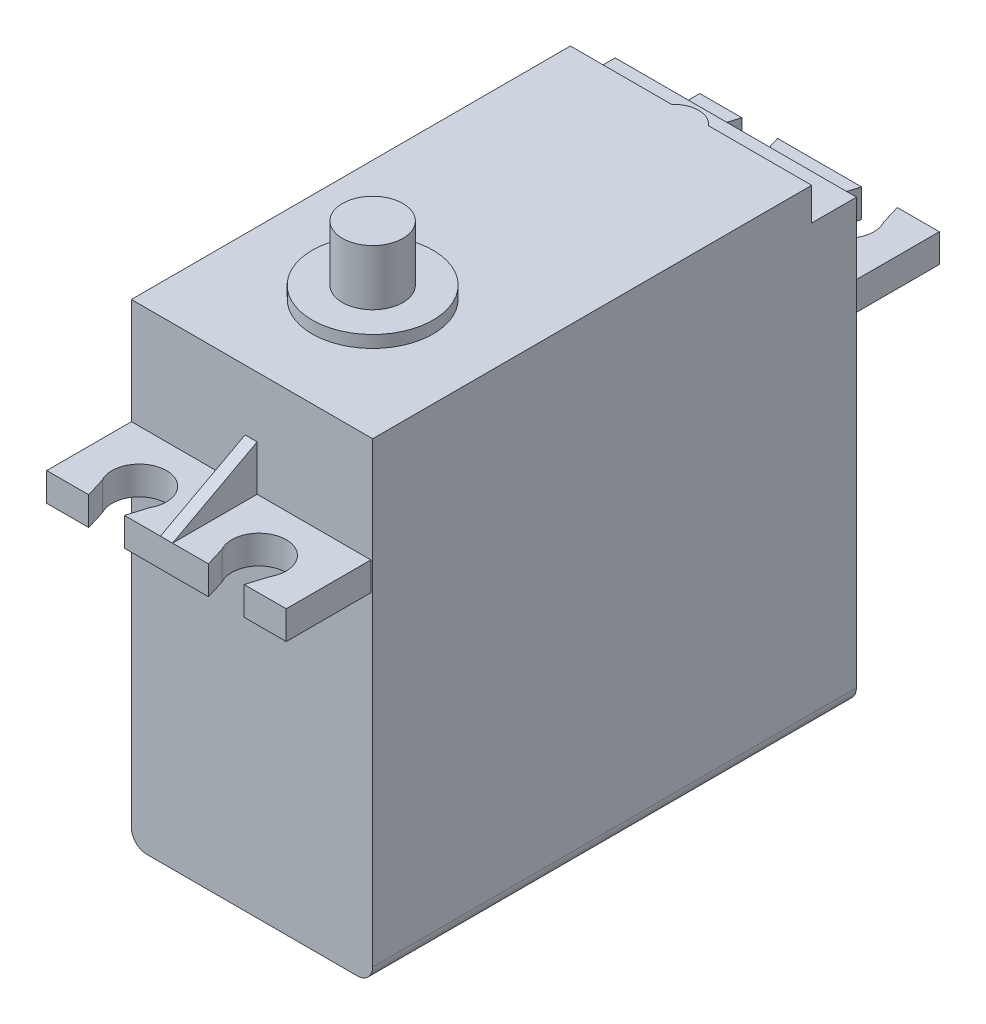
SolidWorks part; units mm, degrees
material "Default"
ref_plane "Top" through (0, 0, 0) normal (0, 0, 1) x (1, 0, 0)
ref_plane "Right" through (0, 0, 0) normal (0, 1, 0) x (1, 0, 0)
ref_plane "Front" through (0, 0, 0) normal (1, 0, 0) x (0, 0, -1)
sketch "Sketch1" plane through (0, 0, 0) normal (0, 0, 1) x (1, 0, 0)
  line L0 (1.27, 0) -> (18.68, 0)
  line L1 (19.95, 1.27) -> (19.95, 36.4)
  line L2 (19.95, 36.4) -> (0, 36.4)
  line L3 (0, 36.4) -> (0, 1.27)
  arc A0 (0, 1.27) -> (1.27, 0) centre (1.27, 1.27) ccw
  arc A1 (18.68, 0) -> (19.95, 1.27) centre (18.68, 1.27) ccw
  point P7 (0, 0)
  point P10 (19.95, 0)
  dimension "D3" = 1.27
  dimension "D1" = 19.95
  dimension "D2" = 36.4
extrude "Boss-Extrude1" add sketch "Sketch1" along normal blind 40
ref_plane "Plane1" through (0, 28, 0) normal (0, -1, 0) x (-1, 0, 0)
sketch "Sketch5" plane through (0, 28, 0) normal (0, -1, 0) x (-1, 0, 0)
  line L0 (0, 0) -> (0, 7)
  line L1 (0, 7) -> (-3.4704, 7)
  line L2 (-9.9, -3.5099) -> (-9.9, -35.0146) construction
  line L3 (-13.3704, 7) -> (-12.882, 5.3907)
  line L4 (0, -20) -> (-36.4379, -20) construction
  line L5 (-16.3296, 7) -> (-16.818, 5.3907)
  line L6 (-3.4704, 7) -> (-2.982, 5.3907)
  line L7 (-4.95, 4.3) -> (-4.95, 12.8389) construction
  line L8 (-6.4296, 7) -> (-6.918, 5.3907)
  line L9 (-13.3704, 7) -> (-6.4296, 7)
  line L11 (-19.8, 0) -> (0, 0)
  line L12 (-19.8, 7) -> (-16.3296, 7)
  line L13 (-19.8, 0) -> (-19.8, 7)
  line L14 (-16.3296, -47) -> (-16.818, -45.3907)
  line L15 (-13.3704, -47) -> (-12.882, -45.3907)
  line L16 (-6.4296, -47) -> (-6.918, -45.3907)
  line L17 (-3.4704, -47) -> (-2.982, -45.3907)
  line L18 (0, -40) -> (0, -47)
  line L19 (-19.8, -40) -> (0, -40)
  line L20 (-19.8, -40) -> (-19.8, -47)
  line L21 (-19.8, -47) -> (-16.3296, -47)
  line L22 (-13.3704, -47) -> (-6.4296, -47)
  line L23 (0, -47) -> (-3.4704, -47)
  arc A0 (-6.918, 5.3907) -> (-2.982, 5.3907) centre (-4.95, 4.3) ccw
  arc A1 (-12.882, 5.3907) -> (-16.818, 5.3907) centre (-14.85, 4.3) cw
  arc A2 (-12.882, -45.3907) -> (-16.818, -45.3907) centre (-14.85, -44.3) ccw
  arc A3 (-6.918, -45.3907) -> (-2.982, -45.3907) centre (-4.95, -44.3) cw
  point P10 (-9.9, 0)
  point P16 (-9.9, 7)
  dimension "D2" = 4.5
  dimension "D1" = 27
  dimension "D3" = 24.3
  dimension "D4" = 9.9
extrude "Boss-Extrude3" add sketch "Sketch5" against normal blind 2.35
sketch "Sketch6" plane through (0, 36.4, 0) normal (0, 1, 0) x (1, 0, 0)
  line L0 (4.95, 4.3) -> (43.7835, 4.3) construction
  line L2 (0, -40) -> (0, 0) construction
  line L3 (19.95, -40) -> (19.95, 0) construction
  line L4 (19.95, -3.7) -> (19.95, -40)
  line L5 (19.95, -40) -> (0, -40)
  line L6 (0, -40) -> (0, -3.7)
  line L7 (9.9, 7) -> (9.9, -14.8948) construction
  line L8 (6.4296, 7) -> (13.3704, 7) construction
  line L9 (-1.8179, -3) -> (23.1241, -3) construction
  line L11 (19.95, 0) -> (0, 0) construction
  line L12 (0, -3.7) -> (8.3801, -3.7)
  line L13 (11.4199, -3.7) -> (19.95, -3.7)
  arc A0 (11.4199, -3.7) -> (8.3801, -3.7) centre (9.9, -5) ccw
  dimension "D1" = 3
extrude "Boss-Extrude4" add sketch "Sketch6" along normal blind 2.7
sketch "Sketch7" plane through (0, 39.1, 0) normal (0, 1, 0) x (1, 0, 0)
  line L0 (4.95, 4.3) -> (14.85, 4.3) construction
  line L1 (9.95, -5.0916) -> (9.95, 20.645) construction
  circle A0 centre (9.95, -30) radius 5
  dimension "D1" = 34.3
  dimension "D2" = 10
extrude "Boss-Extrude5" add sketch "Sketch7" along normal blind 1
sketch "Sketch8" plane through (0, 40.1, 0) normal (0, 1, 0) x (1, 0, 0)
  circle A0 centre (9.95, -30) radius 2.5
extrude "Boss-Extrude6" add sketch "Sketch8" along normal blind 4.6
ref_plane "Plane2" through (9.9, 0, 0) normal (-1, 0, 0) x (0, 0, 1)
sketch "Sketch9" plane through (9.9, 0, 0) normal (-1, 0, 0) x (0, 0, 1)
  line L0 (47, 30.35) -> (40, 34.1)
  line L2 (40, 39.1) -> (40, 30.35) construction
  line L4 (40, 34.1) -> (40, 30.35)
  line L5 (40, 30.35) -> (47, 30.35)
  dimension "D1" = 5
extrude "Boss-Extrude7" add sketch "Sketch9" along normal mid plane 1
